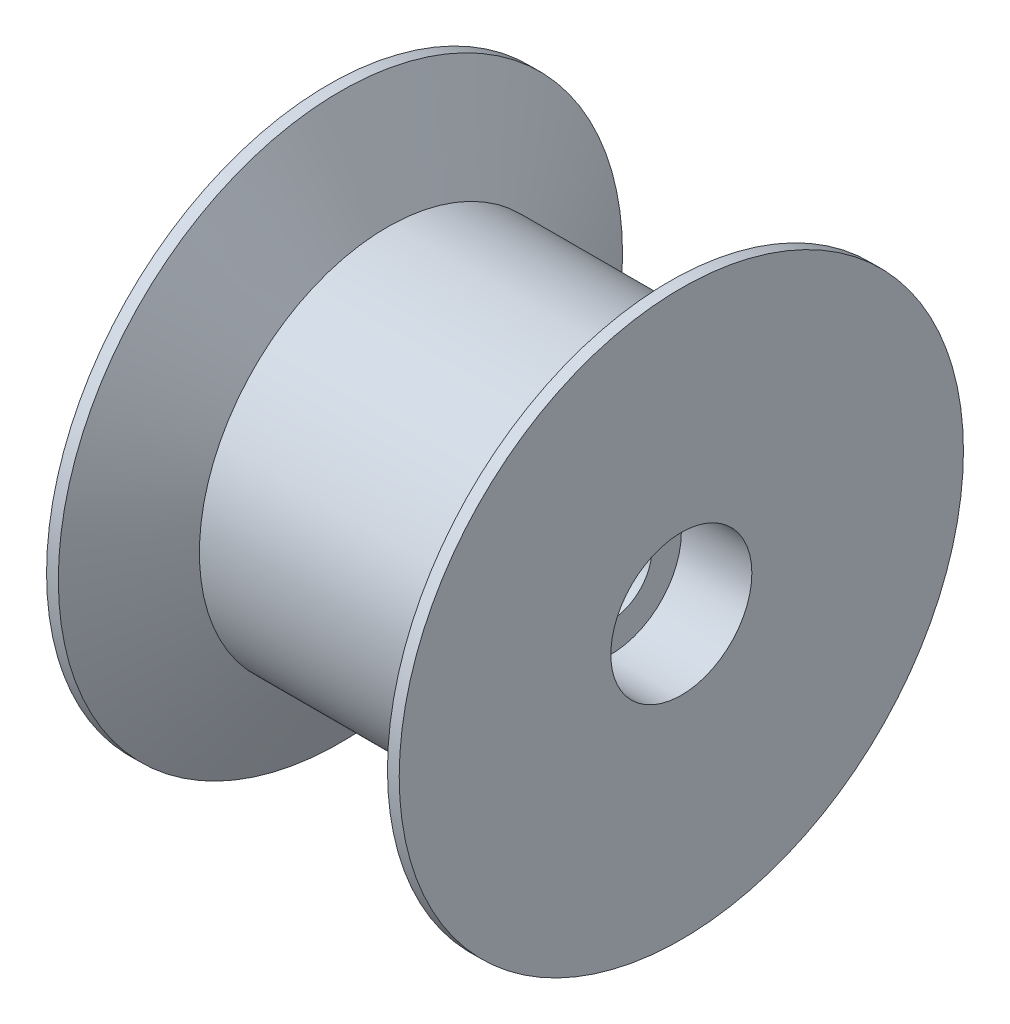
SolidWorks part; units mm, degrees
ref_plane "Plan de face" through (0, 0, 0) normal (0, 0, 1) x (1, 0, 0)
ref_plane "Plan de dessus" through (0, 0, 0) normal (0, 1, 0) x (1, 0, 0)
ref_plane "Plan de droite" through (0, 0, 0) normal (1, 0, 0) x (0, 0, -1)
sketch "Esquisse1" plane through (0, 0, 0) normal (0, 0, 1) x (1, 0, 0)
  line L0 (-7.5, 0) -> (7.5, 0)
  line L1 (7.5, 0) -> (7.5, 12)
  line L2 (7, 12) -> (5, 8)
  line L3 (5, 8) -> (-5, 8)
  line L4 (-5, 8) -> (-7, 12)
  line L5 (-7, 12) -> (-7.5, 12)
  line L8 (0, 0) -> (0, 24.7733) construction
  line L9 (0, 0) -> (-28.9976, 0) construction
  line L10 (7.5, 12) -> (7, 12)
  line L11 (-7.5, 12) -> (-7.5, 0)
  point P9 (0, 0)
  point P11 (-8.1163, 8.7347)
  point P15 (-9.5, 9.7222)
  point P16 (9.9315, 12)
  point P17 (-9.5, 9.969)
  point P18 (-9.9814, 12)
  dimension "D1" = 10
  dimension "D2" = 16
  dimension "D3" = 4
  dimension "D4" = 2
  dimension "D7" = 0.5
revolve "Révolution1" add sketch "Esquisse1" angle 360 about L9
sketch "Esquisse2" plane through (7.5, 0, 0) normal (1, 0, 0) x (0, 0, -1)
  circle A0 centre (0, 0) radius 3
  dimension "D1" = 6
extrude "Enlèv. mat.-Extru.1" cut sketch "Esquisse2" against normal blind 3 contours A0
sketch "Esquisse3" plane through (4.5, 0, 0) normal (1, 0, 0) x (0, 0, -1)
  circle A0 centre (0, 0) radius 1.75
  dimension "D1" = 3.5
extrude "Enlèv. mat.-Extru.2" cut sketch "Esquisse3" against normal through all both and the other way through all
